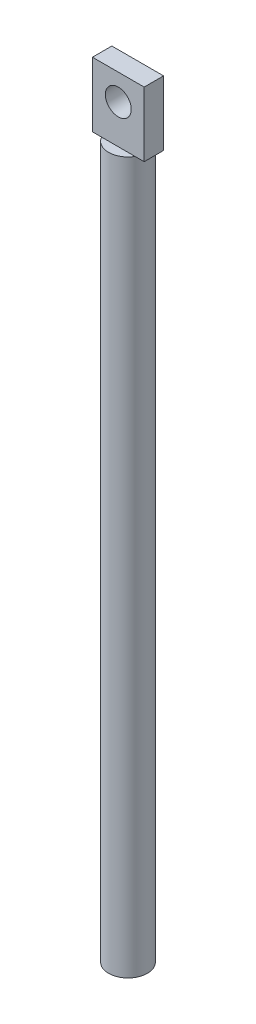
SolidWorks part; units mm, degrees
ref_plane "Front Plane" through (0, 0, 0) normal (0, 0, 1) x (1, 0, 0)
ref_plane "Top Plane" through (0, 0, 0) normal (0, 1, 0) x (1, 0, 0)
ref_plane "Right Plane" through (0, 0, 0) normal (1, 0, 0) x (0, 0, -1)
sketch "Sketch1" plane through (0, 0, 0) normal (0, 1, 0) x (1, 0, 0)
  circle A0 centre (0, 0) radius 1.5
  dimension "D1" = 3
extrude "Boss-Extrude1" add sketch "Sketch1" along normal blind 55
sketch "Sketch2" plane through (0, 55, 0) normal (0, 1, 0) x (1, 0, 0)
  line L1 (-2, 0.75) -> (2, 0.75)
  line L2 (-2, 0.75) -> (-2, -0.75)
  line L3 (-2, -0.75) -> (2, -0.75)
  line L4 (2, 0.75) -> (2, -0.75)
  line L5 (-2, 0.75) -> (2, -0.75) construction
  line L6 (-2, -0.75) -> (2, 0.75) construction
  point P0 (0, 0)
  dimension "D1" = 1.5
  dimension "D2" = 4
extrude "Boss-Extrude2" add sketch "Sketch2" along normal blind 5
sketch "Sketch3" plane through (0, 0, -0.75) normal (0, 0, -1) x (-1, 0, 0)
  line L0 (-2, 60) -> (2, 60) construction
  circle A0 centre (0, 58) radius 1
  dimension "D1" = 2
  dimension "D2" = 2
extrude "Cut-Extrude1" cut sketch "Sketch3" against normal through all
